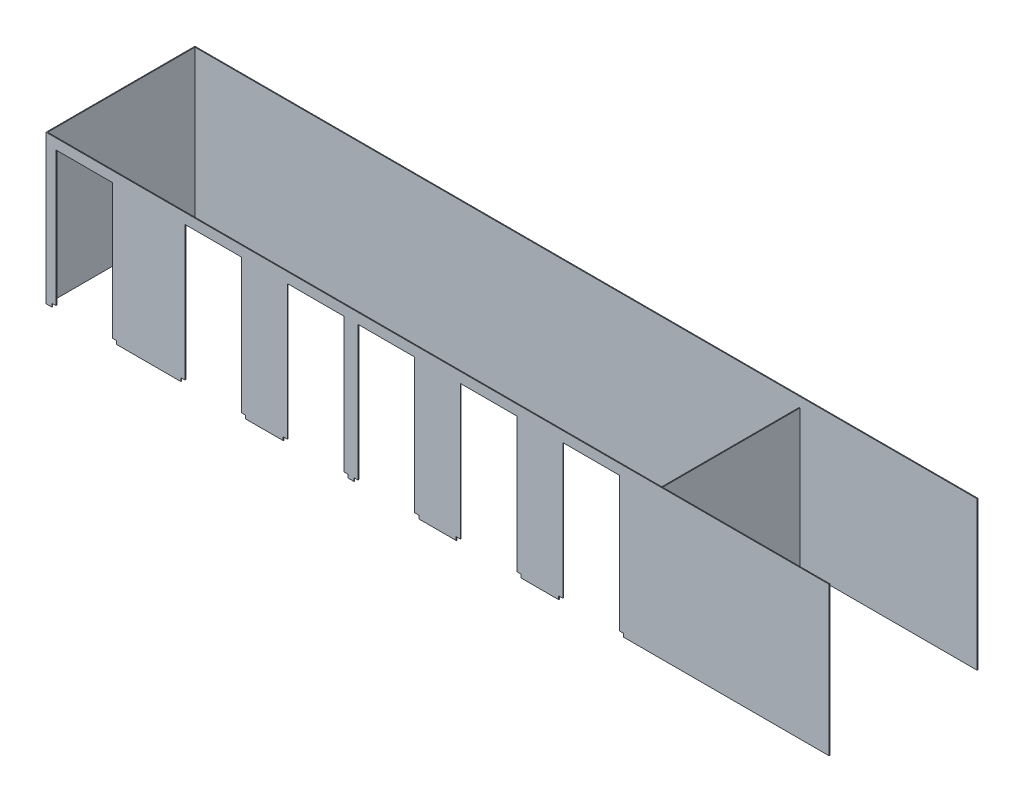
SolidWorks part; units mm, degrees
ref_plane "Front Plane" through (0, 0, 0) normal (0, 0, 1) x (1, 0, 0)
ref_plane "Top Plane" through (0, 0, 0) normal (0, 1, 0) x (1, 0, 0)
ref_plane "Right Plane" through (0, 0, 0) normal (1, 0, 0) x (0, 0, -1)
sketch "Sketch1" plane through (0, 0, 0) normal (0, 1, 0) x (1, 0, 0)
  line L48 (11988.8, 2311.4) -> (11988.8, 2298.7)
  line L49 (11988.8, 50.8) -> (11988.8, 38.1)
  line L141 (11988.8, 38.1) -> (11988.8, 2311.4)
  line L142 (38.1, 38.1) -> (11988.8, 38.1)
  line L143 (38.1, 2311.4) -> (38.1, 38.1)
  line L144 (11988.8, 2311.4) -> (38.1, 2311.4)
  line L146 (38.1, 38.1) -> (11988.8, 38.1)
  line L147 (38.1, 2311.4) -> (38.1, 38.1)
  line L148 (11988.8, 2311.4) -> (38.1, 2311.4)
  line L153 (50.8, 2298.7) -> (50.8, 50.8)
  line L154 (50.8, 50.8) -> (11976.1, 50.8)
  line L155 (11976.1, 50.8) -> (11976.1, 2298.7)
  line L156 (11976.1, 2298.7) -> (50.8, 2298.7)
  line L157 (50.8, 2298.7) -> (50.8, 50.8)
  line L158 (50.8, 50.8) -> (11988.8, 50.8)
  line L160 (11988.8, 2298.7) -> (50.8, 2298.7)
  line L165 (9436.1, 50.8) -> (9436.1, 2146.3)
  line L166 (9423.4, 50.8) -> (9436.1, 50.8)
  line L167 (9423.4, 2146.3) -> (9423.4, 50.8)
  line L168 (9436.1, 2146.3) -> (9423.4, 2146.3)
  line L169 (9436.1, 50.8) -> (9436.1, 2146.3)
  line L170 (9423.4, 50.8) -> (9436.1, 50.8)
  line L171 (9423.4, 2146.3) -> (9423.4, 50.8)
  line L172 (9436.1, 2146.3) -> (9423.4, 2146.3)
  dimension "D1" = 0
  dimension "D2" = 0
  dimension "D3" = 0
extrude "Boss-Extrude1" add sketch "Sketch1" along normal up to surface (2266.95 mm away)
sketch "Sketch2" plane through (0, 0, -38.1) normal (0, 0, 1) x (1, 0, 0)
  line B0 (127, 50.8) -> (127, 0)
  line B1 (127, 0) -> (1117.6, 0)
  line B2 (1117.6, 0) -> (1117.6, 50.8)
  line B3 (1054.1, 50.8) -> (1054.1, 2108.2)
  line B4 (1117.6, 50.8) -> (1054.1, 50.8)
  line B5 (190.5, 50.8) -> (127, 50.8)
  line B6 (190.5, 2108.2) -> (190.5, 50.8)
  line B7 (1054.1, 2108.2) -> (190.5, 2108.2)
  line B8 (2095.5, 50.8) -> (2095.5, 0)
  line B9 (2095.5, 0) -> (3086.1, 0)
  line B10 (3086.1, 0) -> (3086.1, 50.8)
  line B11 (3022.6, 50.8) -> (3022.6, 2108.2)
  line B12 (3086.1, 50.8) -> (3022.6, 50.8)
  line B13 (2159, 50.8) -> (2095.5, 50.8)
  line B14 (2159, 2108.2) -> (2159, 50.8)
  line B15 (3022.6, 2108.2) -> (2159, 2108.2)
  line B16 (3657.6, 50.8) -> (3657.6, 0)
  line B17 (3657.6, 0) -> (4648.2, 0)
  line B18 (4648.2, 0) -> (4648.2, 50.8)
  line B19 (4584.7, 50.8) -> (4584.7, 2108.2)
  line B20 (4648.2, 50.8) -> (4584.7, 50.8)
  line B21 (3721.1, 50.8) -> (3657.6, 50.8)
  line B22 (3721.1, 2108.2) -> (3721.1, 50.8)
  line B23 (4584.7, 2108.2) -> (3721.1, 2108.2)
  line B24 (4737.1, 50.8) -> (4737.1, 0)
  line B25 (4737.1, 0) -> (5727.7, 0)
  line B26 (5727.7, 0) -> (5727.7, 50.8)
  line B27 (5664.2, 50.8) -> (5664.2, 2108.2)
  line B28 (5727.7, 50.8) -> (5664.2, 50.8)
  line B29 (4800.6, 50.8) -> (4737.1, 50.8)
  line B30 (4800.6, 2108.2) -> (4800.6, 50.8)
  line B31 (5664.2, 2108.2) -> (4800.6, 2108.2)
  line B32 (6299.2, 50.8) -> (6299.2, 0)
  line B33 (6299.2, 0) -> (7289.8, 0)
  line B34 (7289.8, 0) -> (7289.8, 50.8)
  line B35 (7226.3, 50.8) -> (7226.3, 2108.2)
  line B36 (7289.8, 50.8) -> (7226.3, 50.8)
  line B37 (6362.7, 50.8) -> (6299.2, 50.8)
  line B38 (6362.7, 2108.2) -> (6362.7, 50.8)
  line B39 (7226.3, 2108.2) -> (6362.7, 2108.2)
  line B40 (7861.3, 50.8) -> (7861.3, 0)
  line B41 (7861.3, 0) -> (8851.9, 0)
  line B42 (8851.9, 0) -> (8851.9, 50.8)
  line B43 (8788.4, 50.8) -> (8788.4, 2108.2)
  line B44 (8851.9, 50.8) -> (8788.4, 50.8)
  line B45 (7924.8, 50.8) -> (7861.3, 50.8)
  line B46 (7924.8, 2108.2) -> (7924.8, 50.8)
  line B47 (8788.4, 2108.2) -> (7924.8, 2108.2)
  line M7 (38.1, 0) -> (11988.8, 0)
sketch_block_instance "Block1-1"
sketch_block "Block1"
sketch_block_instance "Block1-2"
sketch_block_instance "Block1-3"
sketch_block_instance "Block1-4"
sketch_block_instance "Block1-5"
sketch_block_instance "Block1-6"
extrude "Cut-Extrude2" cut sketch "Sketch2" against normal up to vertex (12.7 mm away) contours B3 B7 B6 B5 B0 B2 B4 M7 | B11 B15 B14 B13 B8 B10 B12 M7 | B19 B23 B22 B21 B16 B18 B20 M7 | B27 B31 B30 B29 B24 B26 B28 M7 | B35 B39 B38 B37 B32 B34 B36 M7 | B43 B47 B46 B45 B40 B42 B44 M7
